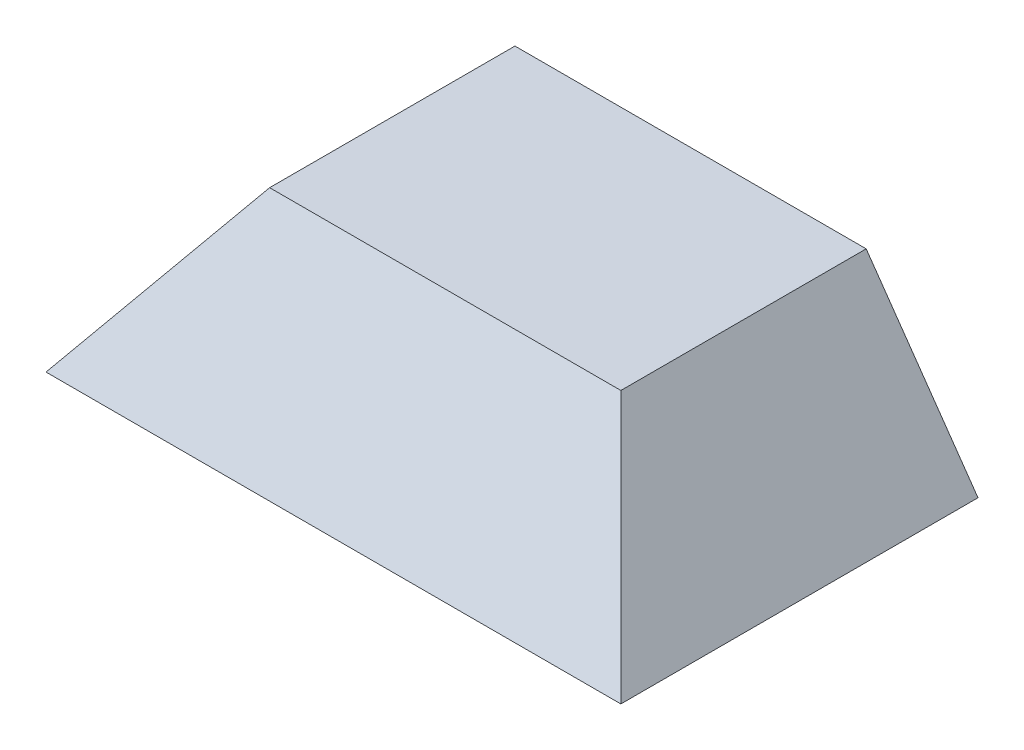
SolidWorks part; units mm, degrees
ref_plane "Alzado" through (0, 0, 0) normal (0, 0, 1) x (1, 0, 0)
ref_plane "Planta" through (0, 0, 0) normal (0, 1, 0) x (1, 0, 0)
ref_plane "Vista lateral" through (0, 0, 0) normal (1, 0, 0) x (0, 0, -1)
sketch "Croquis1" plane through (0, 0, 0) normal (0, 1, 0) x (1, 0, 0)
  line L1 (90, -64.665) -> (-90, -64.665)
  line L2 (90, -64.665) -> (90, 64.665)
  line L3 (90, 64.665) -> (-90, 64.665)
  line L4 (-90, -64.665) -> (-90, 64.665)
  line L5 (90, -64.665) -> (-90, 64.665) construction
  line L6 (90, 64.665) -> (-90, -64.665) construction
  point P0 (0, 0)
  dimension "D1" = 129.33
  dimension "D2" = 180
extrude "Saliente-Extruir1" add sketch "Croquis1" along normal blind 50
sketch "Croquis2" plane through (0, 0, 64.665) normal (0, 0, 1) x (1, 0, 0)
  line L0 (90, 0) -> (54.9896, 50)
  line L1 (-90, 50) -> (90, 50) construction
  line L2 (54.9896, 50) -> (90, 50)
  line L3 (90, 50) -> (90, 0)
  dimension "D1" = 35
extrude "Cortar-Extruir1" cut sketch "Croquis2" against normal up to next
sketch "Croquis4" plane through (-90, 0, 0) normal (-1, 0, 0) x (0, 0, 1)
  line L0 (-64.665, 0) -> (-29.6546, 50)
  line L1 (-64.665, 50) -> (64.665, 50) construction
  line L2 (-29.6546, 50) -> (-64.665, 50)
  line L3 (-64.665, 50) -> (-64.665, 0)
  dimension "D1" = 35
extrude "Cortar-Extruir2" cut sketch "Croquis4" against normal up to next
mirror "Simetría2" about plane through (0, 0, 0) normal (0, 0, 1) of "Cortar-Extruir2"
mirror "Simetría1" about plane through (0, 0, 0) normal (1, 0, 0) of "Cortar-Extruir1" second plane through (0, 0, 0) second plane normal (0, 0, 1)
shell "Vaciado1" thickness 4
sketch "Croquis7" plane through (0, 14.7644, 0) normal (0, 0, -1) x (-1, 0, 0)
  line L0 (-54.9896, 10.2356) -> (-72.4948, 10.2356)
  line L1 (-54.9896, 35.2356) -> (54.9896, 35.2356)
  line L3 (-54.9896, 10.2356) -> (54.9896, 10.2356)
  line L5 (-54.9896, 35.2356) -> (54.9896, 10.2356) construction
  line L6 (-54.9896, 10.2356) -> (54.9896, 35.2356) construction
  line L7 (-54.9896, 35.2356) -> (-90, -14.7644) construction
  line L8 (-72.4948, 10.2356) -> (-54.9896, 35.2356)
  line L9 (54.9896, 10.2356) -> (72.4948, 10.2356)
  line L10 (90, -14.7644) -> (54.9896, 35.2356) construction
  line L11 (72.4948, 10.2356) -> (54.9896, 35.2356)
  point P4 (0, 22.7356)
  dimension "D1" = 25
extrude "Saliente-Extruir4" add sketch "Croquis7" along normal offset from surface (102.5813 mm away) 10
sketch "Croquis14" plane through (0, 0, 0) normal (0, 0, 1) x (1, 0, 0)
  line L0 (-85.1169, 0) -> (-52.8799, 46.0392)
  line L1 (-52.8799, 46.0392) -> (52.9344, 46.0392)
  line L2 (52.9344, 46.0392) -> (85.1169, 0)
  line L3 (85.1169, 0) -> (-85.1169, 0)
extrude "Cortar-Extruir10" cut sketch "Croquis14" against normal offset from surface (92.5813 mm away) 10 up to face at (0, 37.5, -102.5813)
sketch "Croquis15" plane through (0, 0, 0) normal (1, 0, 0) x (0, 0, -1)
  line L0 (47.1598, 0) -> (47.1598, 50)
  line L1 (102.5813, 50) -> (-29.6546, 50) construction
  line L2 (47.1598, 50) -> (102.5813, 50)
  line L3 (102.5813, 50) -> (102.5813, 0)
  line L4 (61.5036, 0) -> (-61.5036, 0) construction
  line L5 (102.5813, 0) -> (47.1598, 0)
extrude "Cortar-Extruir11" cut sketch "Croquis15" against normal through all both and the other way through all
ref_plane "Plano1" through (70, 0, 0) normal (1, 0, 0) x (0, 0, -1)
sketch "Croquis19" plane through (70, 0, 0) normal (1, 0, 0) x (0, 0, -1)
  line L0 (47.1598, 0) -> (0, 0) construction
  line L1 (8.2963, 0) -> (-11.7037, 0)
  line L2 (8.2963, 0) -> (8.2963, 20)
  line L3 (8.2963, 20) -> (-11.7037, 20)
  line L4 (-11.7037, 0) -> (-11.7037, 20)
  line L5 (8.2963, 0) -> (-11.7037, 20) construction
  line L6 (8.2963, 20) -> (-11.7037, 0) construction
  point P4 (-1.7037, 10)
  dimension "D1" = 20
  dimension "D2" = 20
extrude "Saliente-Extruir6" add sketch "Croquis19" along normal up to next
sketch "Croquis20" plane through (70, 0, 0) normal (-1, 0, 0) x (0, 0, 1)
  line L0 (-8.2963, 0) -> (-8.2963, 20) construction
  line L1 (-8.2963, 10) -> (11.7037, 10)
  line L2 (-8.2963, 10) -> (-8.2963, 5)
  line L3 (-8.2963, 5) -> (11.7037, 5)
  line L4 (11.7037, 10) -> (11.7037, 5)
  line L5 (-8.2963, 10) -> (11.7037, 5) construction
  line L6 (-8.2963, 5) -> (11.7037, 10) construction
  line L7 (11.7037, 0) -> (11.7037, 20) construction
  point P4 (1.7037, 7.5)
  dimension "D1" = 5
extrude "Cortar-Extruir14" cut sketch "Croquis20" against normal blind 8
sketch "Croquis22" plane through (0, 5, 0) normal (0, 1, 0) x (1, 0, 0)
  line L0 (78, -1.7037) -> (70, -1.7037) construction
  line L1 (78, 8.2963) -> (78, -11.7037) construction
  line L2 (70, -27.5) -> (70, 27.5) construction
  circle A0 centre (74, -1.7037) radius 1.585
  dimension "D1" = 3.17
extrude "Cortar-Extruir15" cut sketch "Croquis22" against normal up to next
mirror "Simetría3" about plane through (0, 0, 0) normal (1, 0, 0) of "Cortar-Extruir15", "Cortar-Extruir14", "Saliente-Extruir6"
